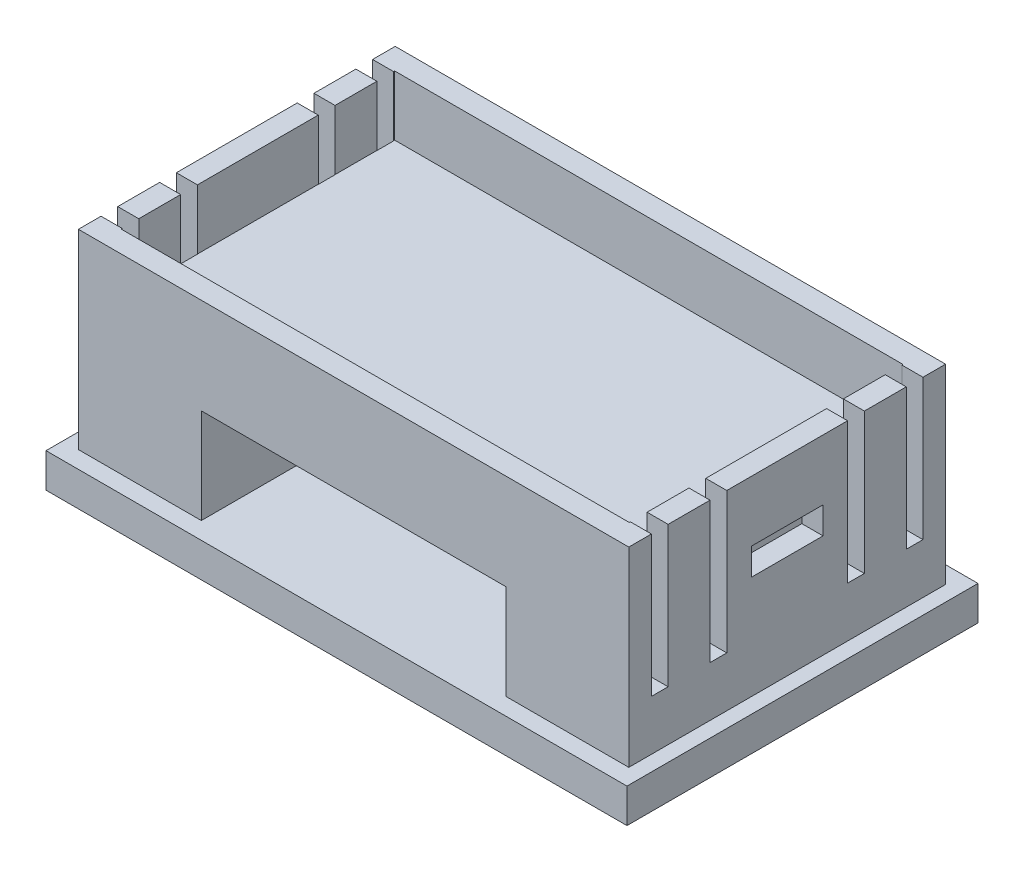
SolidWorks part; units mm, degrees
ref_plane "Front Plane" through (0, 0, 0) normal (0, 0, 1) x (1, 0, 0)
ref_plane "Top Plane" through (0, 0, 0) normal (0, 1, 0) x (1, 0, 0)
ref_plane "Right Plane" through (0, 0, 0) normal (1, 0, 0) x (0, 0, -1)
sketch "Sketch3" plane through (0, 0, 0) normal (0, 1, 0) x (1, 0, 0)
  line L0 (-23.75, 14.35) -> (23.75, -14.35) construction
  line L1 (-23.75, 14.35) -> (23.75, 14.35)
  line L2 (-23.75, 14.35) -> (-23.75, -14.35)
  line L3 (-23.75, -14.35) -> (23.75, -14.35)
  line L4 (23.75, 14.35) -> (23.75, -14.35)
  line L5 (23.75, 14.35) -> (-23.75, -14.35) construction
  point P4 (0, 0)
  dimension "D1" = 28.7
  dimension "D2" = 47.5
extrude "Boss-Extrude2" add sketch "Sketch3" along normal blind 2.8
sketch "Sketch4" plane through (0, 2.8, 0) normal (0, 1, 0) x (1, 0, 0)
  line L0 (-22.5, 12.95) -> (22.5, -12.95) construction
  line L1 (-22.5, 12.95) -> (22.5, 12.95)
  line L2 (-22.5, 12.95) -> (-22.5, -12.95)
  line L3 (-22.5, -12.95) -> (22.5, -12.95)
  line L4 (22.5, 12.95) -> (22.5, -12.95)
  line L5 (22.5, 12.95) -> (-22.5, -12.95) construction
  point P8 (0, 0)
  dimension "D1" = 25.9
  dimension "D2" = 45
extrude "Boss-Extrude3" add sketch "Sketch4" along normal blind 15.6
sketch "Sketch5" plane through (0, 0, 0) normal (0, 0, 1) x (1, 0, 0)
  line L0 (-23.75, 2.8) -> (23.75, 2.8) construction
  line L1 (-12.45, 10.57) -> (12.45, 10.57)
  line L2 (-12.45, 10.57) -> (-12.45, 2.8)
  line L3 (-12.45, 2.8) -> (12.45, 2.8)
  line L4 (12.45, 10.57) -> (12.45, 2.8)
  line L7 (-12.45, 10.57) -> (12.45, 2.8) construction
  line L8 (12.45, 10.57) -> (-12.45, 2.8) construction
  point P6 (0, 6.685)
  dimension "D1" = 24.9
  dimension "D2" = 7.77
extrude "Cut-Extrude1" cut sketch "Sketch5" against normal up to next (12.95 mm away)
mirror "Mirror1" about plane through (0, 0, 0) normal (0, 0, 1) of "Cut-Extrude1"
sketch "Sketch6" plane through (0, 18.4, 0) normal (0, 1, 0) x (1, 0, 0)
  line L0 (22.5, 12.95) -> (-22.5, 12.95) construction
  line L1 (-20.78, 11.19) -> (20.78, 11.19)
  line L2 (-20.78, 11.19) -> (-20.78, -11.19)
  line L3 (-20.78, -11.19) -> (20.78, -11.19)
  line L4 (20.78, 11.19) -> (20.78, -11.19)
  line L5 (-22.5, -12.95) -> (22.5, -12.95) construction
  line L6 (-22.5, 12.95) -> (-22.5, -12.95) construction
  line L7 (22.5, -12.95) -> (22.5, 12.95) construction
  dimension "D1" = 1.76
  dimension "D2" = 1.76
  dimension "D3" = 1.72
  dimension "D4" = 1.72
extrude "Cut-Extrude2" cut sketch "Sketch6" against normal blind 4.9
sketch "Sketch7" plane through (22.5, 0, 0) normal (1, 0, 0) x (0, 0, -1)
  line L0 (-12.95, 18.4) -> (12.95, 18.4) construction
  line L1 (4.94, 18.4) -> (6.31, 18.4)
  line L2 (4.94, 18.4) -> (4.94, 6.9)
  line L3 (4.94, 6.9) -> (6.31, 6.9)
  line L4 (6.31, 18.4) -> (6.31, 6.9)
  line L5 (12.95, 18.4) -> (12.95, 2.8) construction
  line L6 (9.7357, 18.4) -> (11.1, 18.4)
  line L7 (-2.93, 13.45) -> (2.93, 13.45)
  line L12 (-2.93, 11.25) -> (2.93, 11.25)
  line L13 (2.93, 13.45) -> (2.93, 11.25)
  line L14 (9.7357, 18.4) -> (9.7357, 6.9)
  line L15 (9.7357, 6.9) -> (11.1, 6.9)
  line L16 (11.1, 18.4) -> (11.1, 6.9)
  line L17 (-2.93, 13.45) -> (-2.93, 11.25)
  line L18 (-4.94, 6.9) -> (-6.31, 6.9)
  line L19 (-6.31, 18.4) -> (-6.31, 6.9)
  line L20 (-4.94, 18.4) -> (-6.31, 18.4)
  line L21 (-4.94, 18.4) -> (-4.94, 6.9)
  line L22 (-9.7357, 18.4) -> (-9.7357, 6.9)
  line L23 (-9.7357, 6.9) -> (-11.1, 6.9)
  line L24 (-11.1, 18.4) -> (-11.1, 6.9)
  line L25 (-9.7357, 18.4) -> (-11.1, 18.4)
  point P8 (5.625, 6.9)
  dimension "D1" = 6.64
  dimension "D2" = 1.37
  dimension "D3" = 11.5
  dimension "D4" = 2.2
  dimension "D6" = 4.95
  dimension "D7" = 1.85
extrude "Cut-Extrude4" cut sketch "Sketch7" against normal blind 1.73
mirror "Mirror2" about plane through (0, 0, 0) normal (1, 0, 0) of "Cut-Extrude4"
